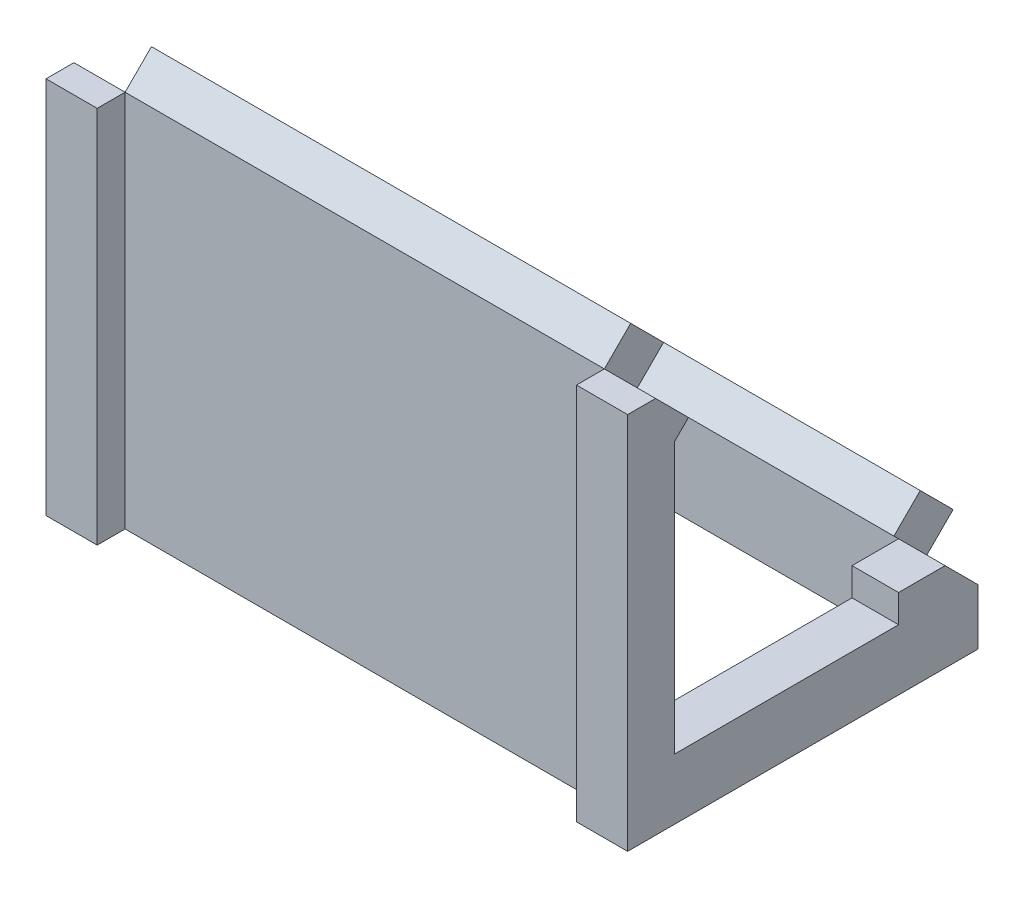
SolidWorks part; units mm, degrees
other "Markup1"
sketch "Sketch33" plane through (0, 74.9533, -74.9533) normal (0.1304, 0.6391, -0.758) x (-0.8301, -0.3477, -0.436)
ref_plane "Front Plane" through (0, 0, 0) normal (0, 0, 1) x (1, 0, 0)
ref_plane "Top Plane" through (0, 0, 0) normal (0, 1, 0) x (1, 0, 0)
ref_plane "Right Plane" through (0, 0, 0) normal (1, 0, 0) x (0, 0, -1)
sketch "Sketch1" plane through (0, 0, 0) normal (1, 0, 0) x (0, 0, -1)
  line L0 (0, 0) -> (69.2965, 0)
  line L1 (69.2965, 0) -> (0, 69.2965)
  line L2 (0, 69.2965) -> (0, 0)
  dimension "D1" = 45
  dimension "D2" = 98
extrude "Boss-Extrude3" add sketch "Sketch1" against normal blind 125
sketch "Sketch3" plane through (0, 0, 0) normal (0, -1, 0) x (1, 0, 0)
  line L1 (0, -69.2965) -> (-125, -69.2965)
  line L2 (0, -69.2965) -> (0, 0)
  line L3 (0, 0) -> (-125, 0)
  line L4 (-125, -69.2965) -> (-125, 0)
  line L5 (0, -69.2965) -> (-125, 0) construction
  line L6 (0, 0) -> (-125, -69.2965) construction
  point P4 (-62.5, -34.6482)
extrude "Boss-Extrude5" add sketch "Sketch3" along normal blind 12
sketch "Sketch6" plane through (-125, 0, 0) normal (-1, 0, 0) x (0, 0, 1)
  line L0 (-69.2965, 0) -> (-62.2254, 7.0711)
  line L1 (-69.2965, 0) -> (0, 69.2965) construction
  line L2 (0, 69.2965) -> (-7.0711, 62.2254)
  line L3 (-62.2254, 7.0711) -> (-7.0711, 7.0711)
  line L4 (-7.0711, 7.0711) -> (-7.0711, 62.2254)
  line L5 (-62.2254, 7.0711) -> (-7.0711, 62.2254)
  line M2 (0, 69.2965) -> (-69.2965, 0)
  dimension "D1" = 10
  dimension "D2" = 10
extrude "Cut-Extrude1" cut sketch "Sketch6" against normal through all contours L3 L4 M2
sketch "Sketch7" plane through (0, 34.6482, -34.6482) normal (0, 0.7071, -0.7071) x (1, 0, 0)
  line L0 (0, 39) -> (-10, 39)
  line L1 (0, 39) -> (-125, 39) construction
  line L2 (-125, 39) -> (-115, 39)
  line L3 (-125, 49) -> (0, 49) construction
  line L4 (-10, 39) -> (-115, 39)
  line L5 (-10, 39) -> (-10, 49)
  line L6 (-10, 49) -> (-115, 49)
  line L7 (-115, 39) -> (-115, 49)
  line L8 (-10, 39) -> (-115, 49) construction
  line L9 (-10, 49) -> (-115, 39) construction
  point P10 (-62.5, 44)
  line M3 (-125, 39) -> (0, 39)
  line M5 (0, 49) -> (-125, 49)
  dimension "D1" = 10
  dimension "D2" = 10
extrude "Boss-Extrude6" add sketch "Sketch7" along normal blind 8 contours L7 L5 M3 M5
sketch "Sketch8" plane through (0, 34.6482, -34.6482) normal (0, 0.7071, -0.7071) x (1, 0, 0)
  line L0 (0, -49) -> (-10, -49)
  line L1 (-125, -49) -> (0, -49) construction
  line L2 (-125, -49) -> (-115, -49)
  line L3 (0, -39) -> (-125, -39) construction
  line L4 (-10, -49) -> (-115, -49)
  line L5 (-10, -49) -> (-10, -39)
  line L6 (-10, -39) -> (-115, -39)
  line L7 (-115, -49) -> (-115, -39)
  line L8 (-10, -49) -> (-115, -39) construction
  line L9 (-10, -39) -> (-115, -49) construction
  point P10 (-62.5, -44)
  line M3 (0, -39) -> (-125, -39)
  line M5 (-125, -49) -> (0, -49)
  dimension "D1" = 10
  dimension "D2" = 10
extrude "Boss-Extrude7" add sketch "Sketch8" along normal blind 8 contours L7 L5 M5 M3
sketch "Sketch9" plane through (0, 7.0711, 0) normal (0, 1, 0) x (1, 0, 0)
  line L0 (0, 62.2254) -> (-10, 62.2254)
  line L1 (-125, 62.2254) -> (-115, 62.2254)
  line L2 (0, 7.0711) -> (-125, 7.0711) construction
  line L3 (-10, 62.2254) -> (-115, 62.2254)
  line L4 (-10, 62.2254) -> (-10, 7.0711)
  line L5 (-10, 7.0711) -> (-115, 7.0711)
  line L6 (-115, 62.2254) -> (-115, 7.0711)
  line L7 (-10, 62.2254) -> (-115, 7.0711) construction
  line L8 (-10, 7.0711) -> (-115, 62.2254) construction
  point P10 (-62.5, 34.6482)
  line M2 (-125, 7.0711) -> (0, 7.0711)
  line M5 (-10, 62.2254) -> (-115, 62.2254)
extrude "Cut-Extrude2" cut sketch "Sketch9" against normal through all contours L6 L4 M5 M2
sketch "Sketch11" plane through (0, 7.0711, 0) normal (0, 1, 0) x (1, 0, 0)
  line L1 (0, 62.2254) -> (-10, 62.2254)
  line L2 (0, 62.2254) -> (0, 7.0711)
  line L3 (0, 7.0711) -> (-10, 7.0711)
  line L4 (-10, 62.2254) -> (-10, 7.0711)
  line L5 (0, 62.2254) -> (-10, 7.0711) construction
  line L6 (0, 7.0711) -> (-10, 62.2254) construction
  point P4 (-5, 34.6482)
extrude "Cut-Extrude3" cut sketch "Sketch11" against normal blind 6
sketch "Sketch12" plane through (0, 7.0711, 0) normal (0, 1, 0) x (1, 0, 0)
  line L1 (-115, 62.2254) -> (-125, 62.2254)
  line L2 (-115, 62.2254) -> (-115, 7.0711)
  line L3 (-115, 7.0711) -> (-125, 7.0711)
  line L4 (-125, 62.2254) -> (-125, 7.0711)
  line L5 (-115, 62.2254) -> (-125, 7.0711) construction
  line L6 (-115, 7.0711) -> (-125, 62.2254) construction
  point P4 (-120, 34.6482)
extrude "Cut-Extrude4" cut sketch "Sketch12" against normal blind 6
sketch "Sketch13" plane through (0, 0, -7.0711) normal (0, 0, -1) x (-1, 0, 0)
  line L1 (10, 1.0711) -> (115, 1.0711)
  line L2 (10, 1.0711) -> (10, 62.2254)
  line L3 (10, 62.2254) -> (115, 62.2254)
  line L4 (115, 1.0711) -> (115, 62.2254)
  line L5 (10, 1.0711) -> (115, 62.2254) construction
  line L6 (10, 62.2254) -> (115, 1.0711) construction
  point P4 (62.5, 31.6482)
extrude "Cut-Extrude6" cut sketch "Sketch13" against normal blind 3
sketch "Sketch14" plane through (0, 34.6482, -34.6482) normal (0, 0.7071, -0.7071) x (1, 0, 0)
  line L0 (0, 49) -> (-6.25, 49)
  line L1 (-10, 49) -> (0, 49) construction
  line L2 (-6.25, 49) -> (-6.25, 42.75)
  circle A0 centre (-6.25, 42.75) radius 1.9
  dimension "D1" = 6.25
  dimension "D2" = 6.25
extrude "Cut-Extrude8" cut sketch "Sketch14" against normal blind 6
ref_plane "Plane1" through (-62.5, 0, 0) normal (1, 0, 0) x (0, 0, -1)
mirror "Mirror1" about plane through (-62.5, 0, 0) normal (1, 0, 0) of "Cut-Extrude8"
sketch "Sketch15" plane through (0, 34.6482, -34.6482) normal (0, 0.7071, -0.7071) x (1, 0, 0)
  line L0 (0, -49) -> (-6.25, -49)
  line L1 (-10, -49) -> (0, -49) construction
  line L2 (-6.25, -49) -> (-6.25, -42.75)
  circle A0 centre (-6.25, -42.75) radius 1.9
  dimension "D3" = 3.8
  dimension "D1" = 6.25
  dimension "D2" = 6.25
extrude "Cut-Extrude9" cut sketch "Sketch15" against normal blind 6
mirror "Mirror2" about plane through (-62.5, 0, 0) normal (1, 0, 0) of "Cut-Extrude9"
sketch "Sketch22" plane through (-10, 0, 0) normal (-1, 0, 0) x (0, 0, 1)
  line L0 (-7.0711, 62.2254) -> (-4.0711, 59.2254)
  line L1 (-4.0711, 62.2254) -> (-4.0711, 1.0711) construction
  line L2 (-4.0711, 59.2254) -> (-4.0711, 62.2254)
  line L3 (-4.0711, 62.2254) -> (-7.0711, 62.2254)
  line L4 (-12.7279, 67.8823) -> (-7.0711, 62.2254) construction
extrude "Boss-Extrude9" add sketch "Sketch22" along normal up to next
sketch "Sketch25" plane through (0, 0, -62.2254) normal (0, 0, 1) x (1, 0, 0)
  line L1 (-10, 1.0711) -> (0, 1.0711)
  line L2 (-10, 1.0711) -> (-10, 7.0711)
  line L3 (-10, 7.0711) -> (0, 7.0711)
  line L4 (0, 1.0711) -> (0, 7.0711)
  line L5 (-10, 1.0711) -> (0, 7.0711) construction
  line L6 (-10, 7.0711) -> (0, 1.0711) construction
  line L7 (-125, 1.0711) -> (-115, 1.0711)
  line L8 (-125, 1.0711) -> (-125, 7.0711)
  line L9 (-125, 7.0711) -> (-115, 7.0711)
  line L10 (-115, 1.0711) -> (-115, 7.0711)
  line L11 (-125, 1.0711) -> (-115, 7.0711) construction
  line L12 (-125, 7.0711) -> (-115, 1.0711) construction
  point P4 (-5, 4.0711)
  point P11 (-120, 4.0711)
extrude "Boss-Extrude13" add sketch "Sketch25" along normal blind 10
sketch "Sketch26" plane through (-10, 0, 0) normal (1, 0, 0) x (0, 0, -1)
  line L0 (0, 69.2965) -> (7.0711, 62.2254)
  line L1 (7.0711, 62.2254) -> (12.7279, 67.8823)
  line L2 (12.7279, 67.8823) -> (5.6569, 74.9533)
  line L3 (5.6569, 74.9533) -> (0, 69.2965)
extrude "Cut-Extrude10" cut sketch "Sketch26" against normal blind 1
sketch "Sketch27" plane through (-10, 0, 0) normal (1, 0, 0) x (0, 0, -1)
  line L0 (62.2254, 7.0711) -> (69.2965, 0)
  line L1 (69.2965, 0) -> (74.9533, 5.6569)
  line L2 (74.9533, 5.6569) -> (67.8823, 12.7279)
  line L3 (67.8823, 12.7279) -> (62.2254, 7.0711)
extrude "Cut-Extrude11" cut sketch "Sketch27" against normal blind 1
mirror "Mirror3" about plane through (-62.5, 0, 0) normal (1, 0, 0) of "Cut-Extrude11", "Cut-Extrude10"
sketch "Sketch29" plane through (0, 0, 0) normal (0, 0, 1) x (1, 0, 0)
  line L0 (-11, 69.2965) -> (0, 69.2965)
  line L1 (0, 69.2965) -> (0, -12)
  line L2 (0, -12) -> (-11, -12)
  line L3 (0, -12) -> (-125, -12) construction
  line L4 (-11, -12) -> (-11, 69.2965)
extrude "Boss-Extrude15" add sketch "Sketch29" along normal blind 6
mirror "Mirror4" about plane through (-62.5, 0, 0) normal (1, 0, 0) of "Boss-Extrude15"
sketch "Sketch31" plane through (0, 34.6482, -34.6482) normal (0, 0.7071, -0.7071) x (1, 0, 0)
  circle A0 centre (-6.25, 42.75) radius 2
  dimension "D1" = 4
extrude "Cut-Extrude16" cut sketch "Sketch31" against normal blind 6
sketch "Sketch32" plane through (0, 34.6482, -34.6482) normal (0, 0.7071, -0.7071) x (1, 0, 0)
  circle A0 centre (-6.25, -42.75) radius 2
  dimension "D1" = 4
extrude "Cut-Extrude17" cut sketch "Sketch32" against normal blind 6
mirror "Mirror5" about plane through (-62.5, 0, 0) normal (1, 0, 0) of "Cut-Extrude17", "Cut-Extrude16"
ref_plane "Plane2" through (-10, 62.2254, -7.0711) normal (1, 0, 0) x (0, 0, -1)
sketch "Sketch41" plane through (-10, 0, 0) normal (-1, 0, 0) x (0, 0, 1)
  line L0 (-7.0711, 1.0711) -> (-4.0711, 1.0711)
  line L1 (-4.0711, 1.0711) -> (-4.0711, 59.2254)
  line L2 (-4.0711, 59.2254) -> (-7.0711, 62.2254)
  line L3 (-7.0711, 62.2254) -> (-4.0711, 59.2254) construction
  line L4 (-7.0711, 62.2254) -> (-7.0711, 1.0711) construction
  line L5 (-7.0711, 62.2254) -> (-7.0711, 1.0711)
extrude "Cut-Extrude22" cut sketch "Sketch41" against normal through all
sketch "Sketch42" plane through (-115, 0, 0) normal (1, 0, 0) x (0, 0, -1)
  line L0 (7.0711, 1.0711) -> (4.0711, 1.0711)
  line L1 (4.0711, 1.0711) -> (4.0711, 59.2254)
  line L2 (4.0711, 59.2254) -> (7.0711, 62.2254)
  line L3 (7.0711, 62.2254) -> (4.0711, 59.2254) construction
  line L4 (7.0711, 1.0711) -> (7.0711, 62.2254) construction
  line L5 (7.0711, 62.2254) -> (7.0711, 1.0711)
extrude "Cut-Extrude23" cut sketch "Sketch42" against normal through all
